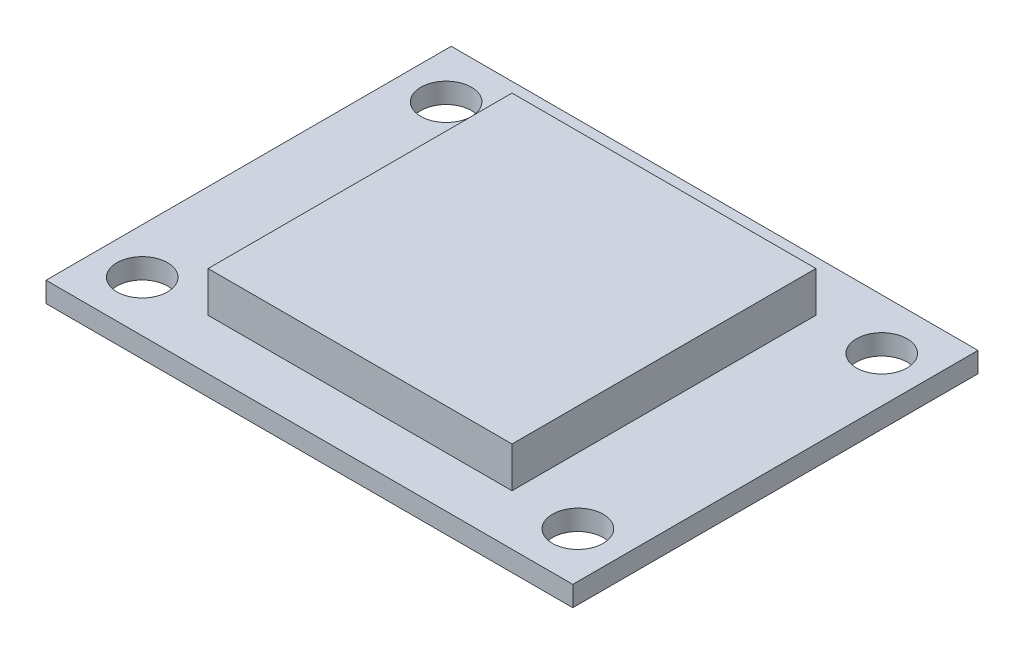
SolidWorks part; units mm, degrees
ref_plane "Front Plane" through (0, 0, 0) normal (0, 0, 1) x (1, 0, 0)
ref_plane "Top Plane" through (0, 0, 0) normal (0, 1, 0) x (1, 0, 0)
ref_plane "Right Plane" through (0, 0, 0) normal (1, 0, 0) x (0, 0, -1)
sketch "Sketch1" plane through (0, 0, 0) normal (0, 1, 0) x (1, 0, 0)
  line L1 (-13, 10) -> (13, 10)
  line L2 (-13, 10) -> (-13, -10)
  line L3 (-13, -10) -> (13, -10)
  line L4 (13, 10) -> (13, -10)
  line L5 (-13, 10) -> (13, -10) construction
  line L6 (-13, -10) -> (13, 10) construction
  point P0 (0, 0)
  dimension "D1" = 26
  dimension "D2" = 20
extrude "Boss-Extrude1" add sketch "Sketch1" along normal blind 1
sketch "Sketch2" plane through (0, 0, 0) normal (0, 1, 0) x (1, 0, 0)
  line L0 (-0.55, 0) -> (0.55, 0) construction
  line L1 (0, -0.55) -> (0, 0.55) construction
  circle A0 centre (-10.75, 7.5) radius 1.25
  circle A4 centre (-10.75, -7.5) radius 1.25
  circle A5 centre (10.75, -7.5) radius 1.25
  circle A6 centre (10.75, 7.5) radius 1.25
  dimension "D1" = 2.5
  dimension "D6" = 7.5
  dimension "D5" = 10.75
extrude "Cut-Extrude1" cut sketch "Sketch2" along normal blind 1
sketch "Sketch3" plane through (0, 0, 0) normal (0, 1, 0) x (1, 0, 0)
  line L1 (-7.5, 7.5) -> (7.5, 7.5)
  line L2 (-7.5, 7.5) -> (-7.5, -7.5)
  line L3 (-7.5, -7.5) -> (7.5, -7.5)
  line L4 (7.5, 7.5) -> (7.5, -7.5)
  line L5 (-7.5, 7.5) -> (7.5, -7.5) construction
  line L6 (-7.5, -7.5) -> (7.5, 7.5) construction
  point P0 (0, 0)
  dimension "D1" = 15
  dimension "D2" = 15
extrude "Boss-Extrude2" add sketch "Sketch3" along normal blind 3
